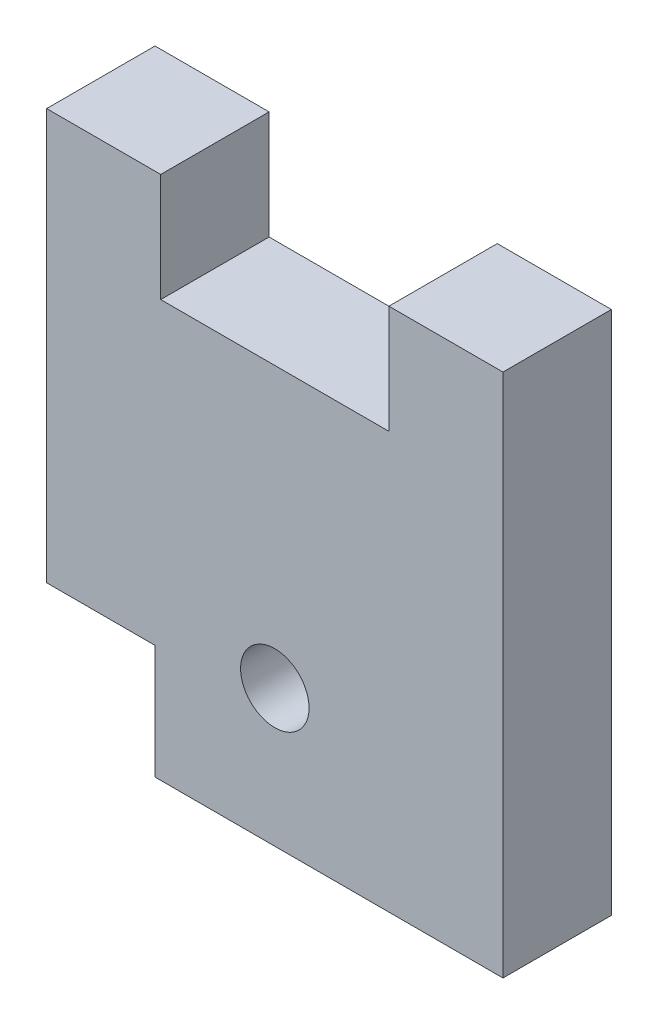
SolidWorks part; units mm, degrees
material "Pine"
ref_plane "Front Plane" through (0, 0, 0) normal (0, 0, 1) x (1, 0, 0)
ref_plane "Top Plane" through (0, 0, 0) normal (0, 1, 0) x (1, 0, 0)
ref_plane "Right Plane" through (0, 0, 0) normal (1, 0, 0) x (0, 0, -1)
sketch "Sketch1" plane through (0, 0, 0) normal (0, 0, 1) x (1, 0, 0)
  line L0 (15, 0) -> (20, 0)
  line L1 (0, 0) -> (5, 0)
  line L2 (0, 0) -> (0, -18)
  line L3 (4.75, -23) -> (20, -23)
  line L4 (20, 0) -> (20, -23)
  line L6 (5, 0) -> (5, -4.75)
  line L7 (5, -4.75) -> (15, -4.75)
  line L8 (15, 0) -> (15, -4.75)
  line L16 (0, -18) -> (4.75, -18)
  line L17 (4.75, -23) -> (4.75, -18)
  circle A0 centre (10, -17) radius 1.5
  point P13 (10, -4.75)
  dimension "D6" = 3
  dimension "D7" = 12.25
  dimension "D1" = 5
  dimension "D2" = 5
  dimension "D3" = 10
  dimension "D4" = 4.75
  dimension "D5" = 23
  dimension "D8" = 4.75
  dimension "D9" = 5
extrude "Boss-Extrude1" add sketch "Sketch1" along normal blind 4.75
